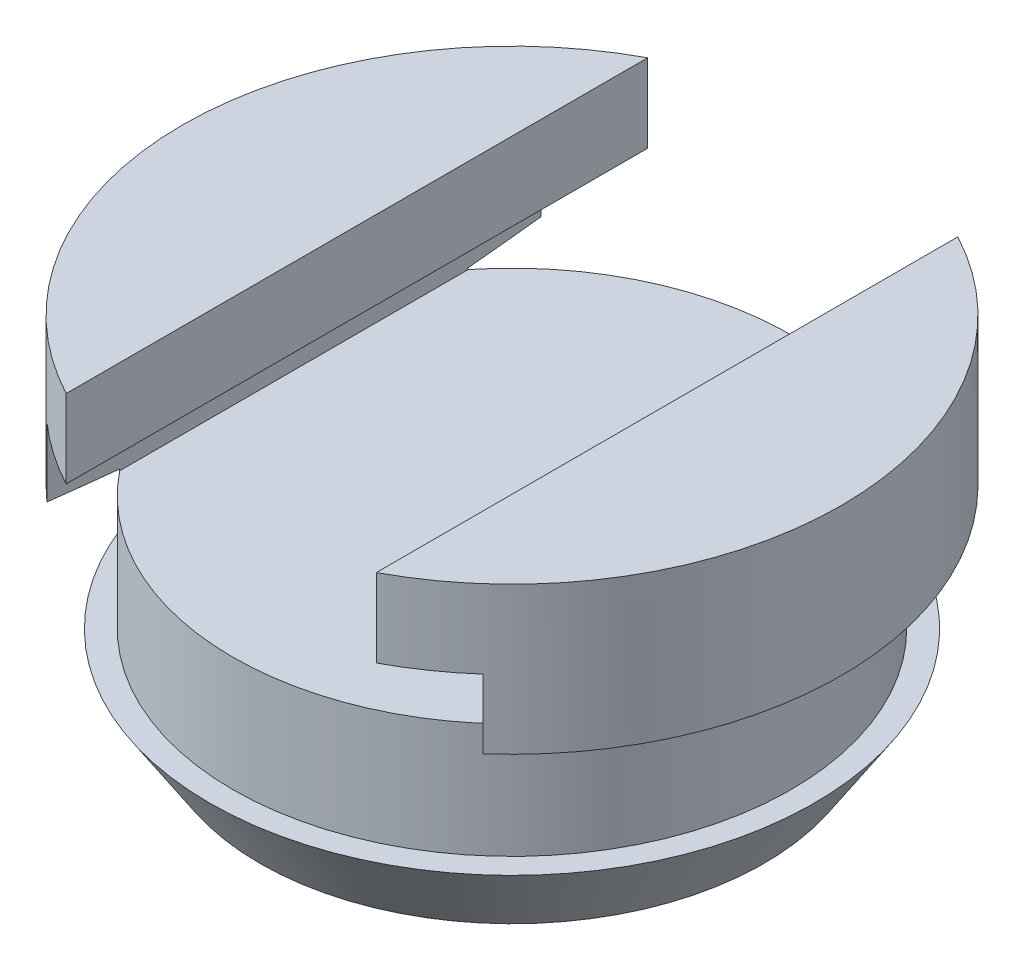
SolidWorks part; units mm, degrees
ref_plane "Front Plane" through (0, 0, 0) normal (0, 0, 1) x (1, 0, 0)
ref_plane "Top Plane" through (0, 0, 0) normal (0, 1, 0) x (1, 0, 0)
ref_plane "Right Plane" through (0, 0, 0) normal (1, 0, 0) x (0, 0, -1)
sketch "Sketch1" plane through (0, 0, 0) normal (0, 0, 1) x (1, 0, 0)
  line L0 (0, 0) -> (-8.255, 0)
  line L2 (-10.795, 11.43) -> (0, 11.43)
  line L3 (0, 11.43) -> (0, 0)
  line L4 (-10.795, 6.604) -> (-9.144, 6.35)
  line L5 (-9.144, 6.35) -> (-9.144, 2.54)
  line L6 (-9.144, 2.54) -> (-9.906, 2.54)
  line L7 (-10.795, 6.604) -> (-10.795, 11.43)
  line L8 (-9.906, 2.54) -> (-8.255, 0)
  dimension "D1" = 9.144
  dimension "D2" = 10.795
revolve "Revolve1" add sketch "Sketch1" angle 360 about L3
sketch "Sketch2" plane through (0, 0, 0) normal (0, 0, 1) x (1, 0, 0)
  line L0 (7.1437, 6.2986) -> (-7.1437, 6.2986)
  line L1 (-7.1437, 6.2986) -> (-7.1437, 8.864)
  line L2 (-7.1437, 8.864) -> (-5.08, 8.864)
  line L3 (-5.08, 8.864) -> (-5.08, 11.43)
  line L4 (-5.08, 11.43) -> (5.08, 11.43)
  line L5 (0, 0) -> (0, 13.4956) construction
  line L6 (5.08, 8.864) -> (5.08, 11.43)
  line L7 (7.1437, 8.864) -> (5.08, 8.864)
  line L8 (7.1437, 6.2986) -> (7.1437, 8.864)
  line L9 (10.795, 11.43) -> (-10.795, 11.43) construction
  point P9 (0, 11.43)
  point P13 (0, 6.2986)
  dimension "D1" = 10.16
  dimension "D2" = 14.2875
extrude "Cut-Extrude1" cut sketch "Sketch2" against normal mid plane 38.1
